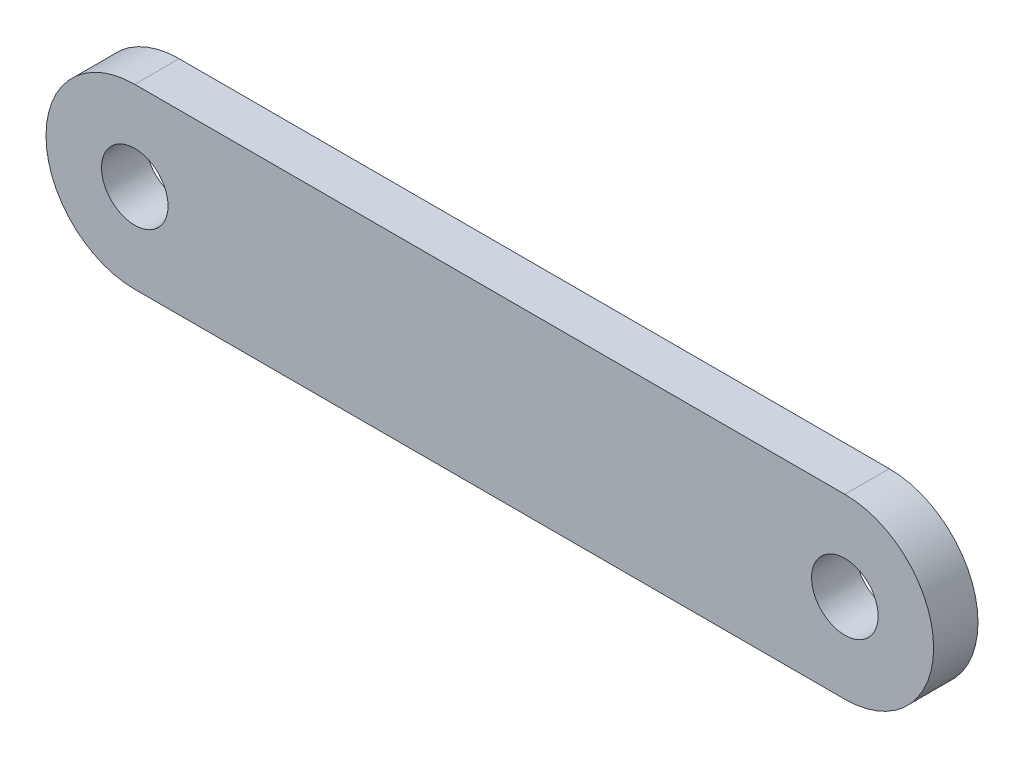
SolidWorks part; units mm, degrees
ref_plane "Front Plane" through (0, 0, 0) normal (0, 0, 1) x (1, 0, 0)
ref_plane "Top Plane" through (0, 0, 0) normal (0, 1, 0) x (1, 0, 0)
ref_plane "Right Plane" through (0, 0, 0) normal (1, 0, 0) x (0, 0, -1)
sketch "Sketch1" plane through (0, 0, 0) normal (0, 0, 1) x (1, 0, 0)
  line L0 (-50.8, 0) -> (50.8, 0) construction
  line L1 (-50.8, 12.7) -> (50.8, 12.7)
  line L2 (-50.8, -12.7) -> (50.8, -12.7)
  arc A0 (-50.8, 12.7) -> (-50.8, -12.7) centre (-50.8, 0) ccw
  arc A1 (50.8, -12.7) -> (50.8, 12.7) centre (50.8, 0) ccw
  circle A2 centre (-50.8, 0) radius 4.7625
  circle A3 centre (50.8, 0) radius 4.7625
  point P3 (0, 0)
  dimension "D1" = 9.525
  dimension "D2" = 101.6
  dimension "D3" = 25.4
extrude "Boss-Extrude1" add sketch "Sketch1" along normal blind 6.35
